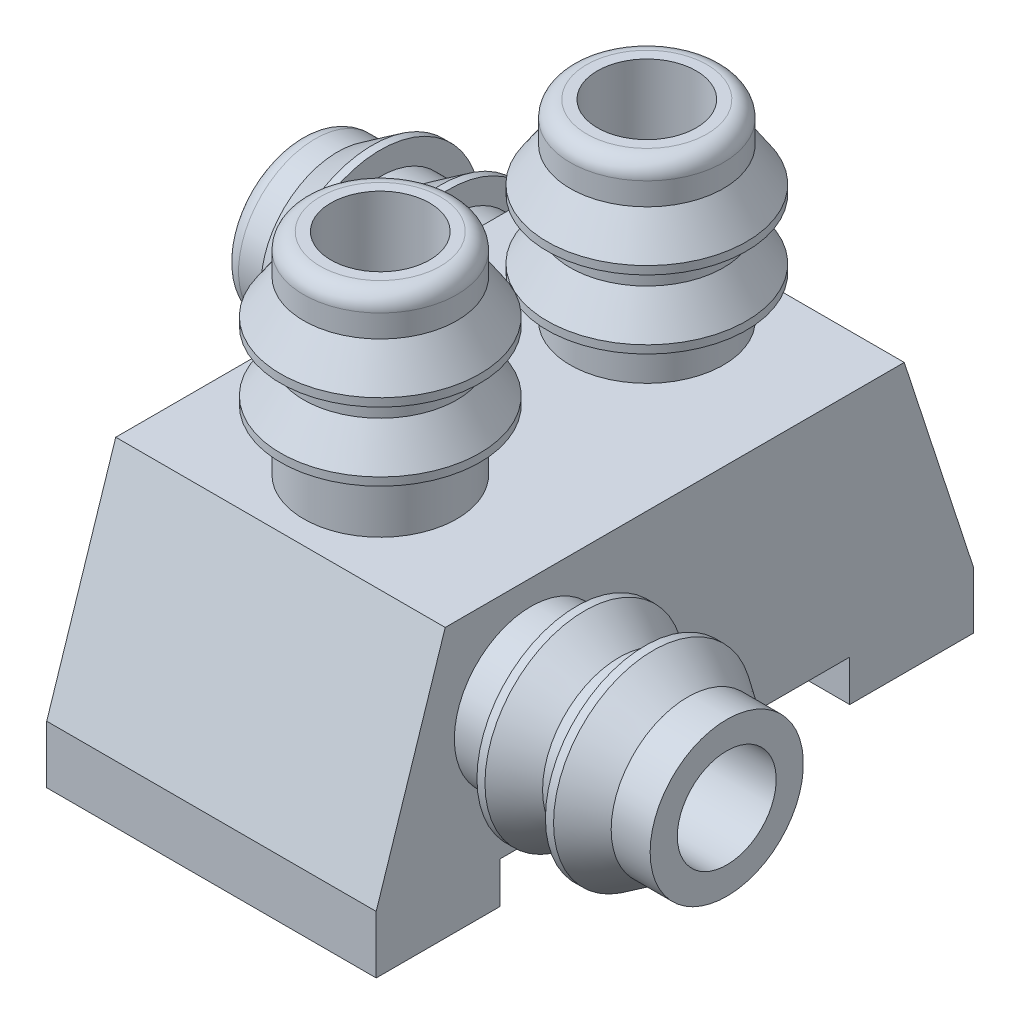
SolidWorks part; units mm, degrees
ref_plane "Front Plane" through (0, 0, 0) normal (0, 0, 1) x (1, 0, 0)
ref_plane "Top Plane" through (0, 0, 0) normal (0, 1, 0) x (1, 0, 0)
ref_plane "Right Plane" through (0, 0, 0) normal (1, 0, 0) x (0, 0, -1)
sketch "Sketch3" plane through (0, 0, 0) normal (1, 0, 0) x (0, 0, -1)
  line L0 (-20.1231, -5.7709) -> (-14.5502, -5.7709)
  line L1 (-20.961, -8.3376) -> (-20.1231, -5.7709)
  line L2 (-15.2123, -8.5376) -> (-15.2123, -9.0376)
  line L3 (-15.2123, -9.0376) -> (-13.7123, -9.0376)
  line L4 (-13.7123, -9.0376) -> (-13.7123, -8.3376)
  line L5 (-13.7123, -8.3376) -> (-14.5502, -5.7709)
  line L6 (-20.961, -9.0376) -> (-20.961, -8.3376)
  line L7 (-19.461, -9.0376) -> (-20.961, -9.0376)
  line L9 (-17.3366, -6.3376) -> (-17.3366, -10.0275) construction
  line L10 (-19.461, -8.5376) -> (-19.461, -9.0376)
  line L12 (-19.461, -8.5376) -> (-15.2123, -8.5376)
extrude "Boss-Extrude2" add sketch "Sketch3" along normal blind 4
ref_plane "Plane1" through (2, 0, 0) normal (1, 0, 0) x (0, 0, -1)
sketch "Sketch4" plane through (2, 0, 0) normal (1, 0, 0) x (0, 0, -1)
  line L0 (-20.8207, -8.0064) -> (-20.7132, -7.6942)
  line L1 (-22.6671, -7.3707) -> (-22.3611, -7.7718)
  line L2 (-21.8797, -7.6418) -> (-21.5736, -8.043)
  line L3 (-23.007, -6.9044) -> (-23.1145, -7.2166)
  line L4 (-23.007, -6.9044) -> (-20.7132, -7.6942)
  line L5 (-21.3907, -7.8102) -> (-20.8207, -8.0064)
  line L6 (-22.1767, -7.5395) -> (-21.8797, -7.6418)
  line L7 (-22.6671, -7.3707) -> (-23.1145, -7.2166)
  line L8 (-22.3611, -7.7718) -> (-22.2678, -7.804)
  line L9 (-20.5178, -7.1269) -> (-22.5583, -6.4243) construction
  line L10 (-22.2678, -7.804) -> (-22.1767, -7.5395)
  line L11 (-21.5736, -8.043) -> (-21.4817, -8.0746)
  line L12 (-21.4817, -8.0746) -> (-21.3907, -7.8102)
revolve "Revolve1" [suppressed] add sketch "Sketch4" angle 360 about L9
sketch "Sketch5" plane through (2, 0, 0) normal (1, 0, 0) x (0, 0, -1)
  line L0 (-19.8419, -5.8395) -> (-19.5116, -5.8395)
  line L1 (-19.8419, -3.6867) -> (-20.1216, -4.1066)
  line L2 (-19.8419, -4.5195) -> (-20.1216, -4.9395)
  line L3 (-19.5116, -3.2135) -> (-19.8419, -3.2135)
  line L4 (-19.5116, -3.2135) -> (-19.5116, -5.8395)
  line L5 (-19.8419, -5.0367) -> (-19.8419, -5.8395)
  line L6 (-19.8419, -4.2053) -> (-19.8419, -4.5195)
  line L7 (-19.8419, -3.6867) -> (-19.8419, -3.2135)
  line L8 (-20.1216, -4.1066) -> (-20.1216, -4.2053)
  line L9 (-18.9116, -5.6395) -> (-18.9116, -3.4815) construction
  line L10 (-20.1216, -4.2053) -> (-19.8419, -4.2053)
  line L11 (-20.1216, -4.9395) -> (-20.1216, -5.0367)
  line L12 (-20.1216, -5.0367) -> (-19.8419, -5.0367)
revolve "Revolve2" add sketch "Sketch5" angle 360 about L9
sketch "Sketch6" plane through (2, 0, 0) normal (1, 0, 0) x (0, 0, -1)
  line L0 (-16.6058, -6.0652) -> (-16.2755, -6.0652)
  line L1 (-16.6058, -3.9152) -> (-16.8855, -4.3351)
  line L2 (-16.6058, -4.748) -> (-16.8855, -5.168)
  line L3 (-16.2755, -3.442) -> (-16.6058, -3.442)
  line L4 (-16.2755, -3.442) -> (-16.2755, -6.0652)
  line L5 (-16.6058, -5.2652) -> (-16.6058, -6.0652)
  line L6 (-16.6058, -4.4338) -> (-16.6058, -4.748)
  line L7 (-16.6058, -3.9152) -> (-16.6058, -3.442)
  line L8 (-16.8855, -4.3351) -> (-16.8855, -4.4338)
  line L9 (-15.6755, -6.068) -> (-15.6755, -3.91) construction
  line L10 (-16.8855, -4.4338) -> (-16.6058, -4.4338)
  line L11 (-16.8855, -5.168) -> (-16.8855, -5.2652)
  line L12 (-16.8855, -5.2652) -> (-16.6058, -5.2652)
revolve "Revolve3" add sketch "Sketch6" angle 360 about L9
sketch "Sketch7" plane through (2, 0, 0) normal (1, 0, 0) x (0, 0, -1)
  line L0 (-14.4218, -6.2515) -> (-14.3197, -6.5656)
  line L1 (-12.5645, -5.6481) -> (-13.0504, -5.5119)
  line L2 (-13.3566, -5.9054) -> (-13.8424, -5.7692)
  line L3 (-12.0125, -5.816) -> (-12.1145, -5.5019)
  line L4 (-12.0125, -5.816) -> (-14.3197, -6.5656)
  line L5 (-13.8485, -6.0653) -> (-14.4218, -6.2515)
  line L6 (-13.0578, -5.8084) -> (-13.3566, -5.9054)
  line L7 (-12.5645, -5.6481) -> (-12.1145, -5.5019)
  line L8 (-13.0504, -5.5119) -> (-13.1442, -5.5424)
  line L9 (-14.1343, -7.1363) -> (-12.0819, -6.4694) construction
  line L10 (-13.1442, -5.5424) -> (-13.0578, -5.8084)
  line L11 (-13.8424, -5.7692) -> (-13.9349, -5.7993)
  line L12 (-13.9349, -5.7993) -> (-13.8485, -6.0653)
revolve "Revolve4" [suppressed] add sketch "Sketch7" angle 360 about L9
sketch "Sketch8" [suppressed] plane through (0, 5.3808, 16.4826) normal (0, 0.3103, 0.9506) x (1, 0, 0)
  ellipse E0 centre (1.5, -13.1416) end of major axis (1.5, -13.7417) minor radius 0.6 construction
  ellipse E1 centre (1.5, -13.1416) end of major axis (1.5, -13.7417) minor radius 0.6
extrude "Cut-Extrude2" [suppressed] cut sketch "Sketch8" against normal blind 1.4
sketch "Sketch10" plane through (0, -5.7709, 0) normal (0, 1, 0) x (1, 0, 0)
  circle A0 centre (2, -18.9116) radius 0.6 construction
  circle A1 centre (2, -18.9116) radius 0.6
  circle A2 centre (2, -15.6755) radius 0.6 construction
  circle A3 centre (2, -15.6755) radius 0.6
extrude "Cut-Extrude3" cut sketch "Sketch10" against normal blind 2 contours A1 | A3
fillet "Fillet1" [suppressed] radius 0.5
sketch "Sketch11" [suppressed] plane through (0, -4.8483, 14.8514) normal (0, 0.3103, -0.9506) x (-1, 0, 0)
  circle A0 centre (-1.5, -2.3976) radius 0.6 construction
  circle A1 centre (-1.5, -2.3976) radius 0.6
extrude "Cut-Extrude4" [suppressed] cut sketch "Sketch11" against normal blind 1.4
fillet "Fillet2" [suppressed] radius 0.5
chamfer "Chamfer1" [suppressed] distance 0.09 angle 79
ref_plane "Plane2" through (0, -7, 0) normal (0, 1, 0) x (1, 0, 0)
sketch "Sketch12" plane through (0, -7, 0) normal (0, 1, 0) x (1, 0, 0)
  line L13 (0, -16.4058) -> (0, -16.0755)
  line L14 (-1.9528, -16.4058) -> (-1.5328, -16.6855)
  line L15 (-1.12, -16.4058) -> (-0.7, -16.6855)
  line L16 (-2.426, -16.0755) -> (-2.426, -16.4058)
  line L17 (-2.426, -16.0755) -> (0, -16.0755)
  line L18 (-0.6028, -16.4058) -> (0, -16.4058)
  line L19 (-1.4342, -16.4058) -> (-1.12, -16.4058)
  line L20 (-1.9528, -16.4058) -> (-2.426, -16.4058)
  line L21 (-1.5328, -16.6855) -> (-1.4342, -16.6855)
  line L22 (0, -15.4755) -> (-2.158, -15.4755) construction
  line L23 (-1.4342, -16.6855) -> (-1.4342, -16.4058)
  line L24 (-0.7, -16.6855) -> (-0.6028, -16.6855)
  line L25 (-0.6028, -16.6855) -> (-0.6028, -16.4058)
revolve "Revolve5" add sketch "Sketch12" angle 360 about L22
sketch "Sketch13" plane through (0, -7, 0) normal (0, 1, 0) x (1, 0, 0)
  line L9 (3.9511, -19.0821) -> (6.1091, -19.0821) construction
  line L14 (4.5539, -20.2921) -> (4.5539, -20.0124)
  line L15 (4.6511, -20.2921) -> (4.5539, -20.2921)
  line L16 (5.3853, -20.2921) -> (5.3853, -20.0124)
  line L17 (5.484, -20.2921) -> (5.3853, -20.2921)
  line L18 (5.9039, -20.0124) -> (6.3771, -20.0124)
  line L19 (5.3853, -20.0124) -> (5.0711, -20.0124)
  line L20 (4.5539, -20.0124) -> (3.9511, -20.0124)
  line L21 (6.3771, -19.6821) -> (3.9511, -19.6821)
  line L22 (6.3771, -19.6821) -> (6.3771, -20.0124)
  line L23 (5.0711, -20.0124) -> (4.6511, -20.2921)
  line L24 (5.9039, -20.0124) -> (5.484, -20.2921)
  line L25 (3.9511, -20.0124) -> (3.9511, -19.6821)
revolve "Revolve6" add sketch "Sketch13" angle 360 about L9
sketch "Sketch14" plane through (0, 0, 0) normal (-1, 0, 0) x (0, 0, 1)
  circle A0 centre (15.4755, -7) radius 0.6 construction
  circle A1 centre (15.4755, -7) radius 0.6
extrude "Cut-Extrude5" cut sketch "Sketch14" against normal blind 2.6
sketch "Sketch15" plane through (4, 0, 0) normal (1, 0, 0) x (0, 0, -1)
  circle A0 centre (-19.0821, -7) radius 0.6 construction
  circle A1 centre (-19.0821, -7) radius 0.6
extrude "Cut-Extrude6" cut sketch "Sketch15" against normal blind 3
fillet "Fillet3" radius 0.2 3 edges at (2, -3.2135, 17.9814) (2, -3.442, 14.7453) (-2.426, -7, 14.5453)
